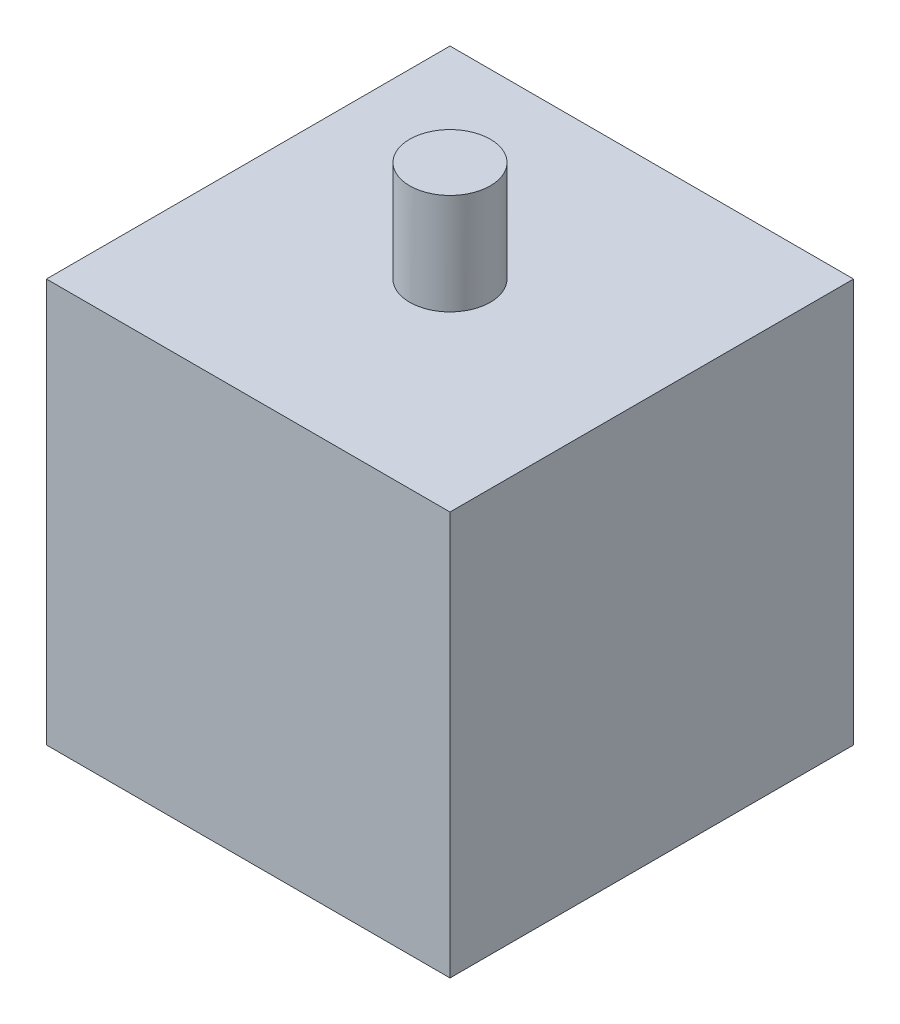
SolidWorks part; units mm, degrees
ref_plane "Front Plane" through (0, 0, 0) normal (0, 0, 1) x (1, 0, 0)
ref_plane "Top Plane" through (0, 0, 0) normal (0, 1, 0) x (1, 0, 0)
ref_plane "Right Plane" through (0, 0, 0) normal (1, 0, 0) x (0, 0, -1)
sketch "Sketch1" plane through (0, 0, 0) normal (0, 1, 0) x (1, 0, 0)
  line L1 (0, 0) -> (100, 0)
  line L2 (0, 0) -> (0, 100)
  line L3 (0, 100) -> (100, 100)
  line L4 (100, 0) -> (100, 100)
  dimension "D1" = 100
  dimension "D2" = 100
extrude "Boss-Extrude1" add sketch "Sketch1" along normal blind 100
sketch "Sketch2" plane through (0, 100, 0) normal (0, 1, 0) x (1, 0, 0)
  line L0 (0, 50) -> (100, 50) construction
  line L4 (0, 100) -> (0, 0)
  line L5 (0, 0) -> (100, 0)
  line L6 (100, 0) -> (100, 100)
  line L7 (100, 100) -> (0, 100)
  line L8 (0, 100) -> (0, 0)
  line L9 (0, 0) -> (100, 0)
  line L10 (100, 0) -> (100, 100)
  line L11 (100, 100) -> (0, 100)
  circle A0 centre (50, 50) radius 10
  dimension "D1" = 0
extrude "Boss-Extrude2" add sketch "Sketch2" along normal blind 25 contours A0
